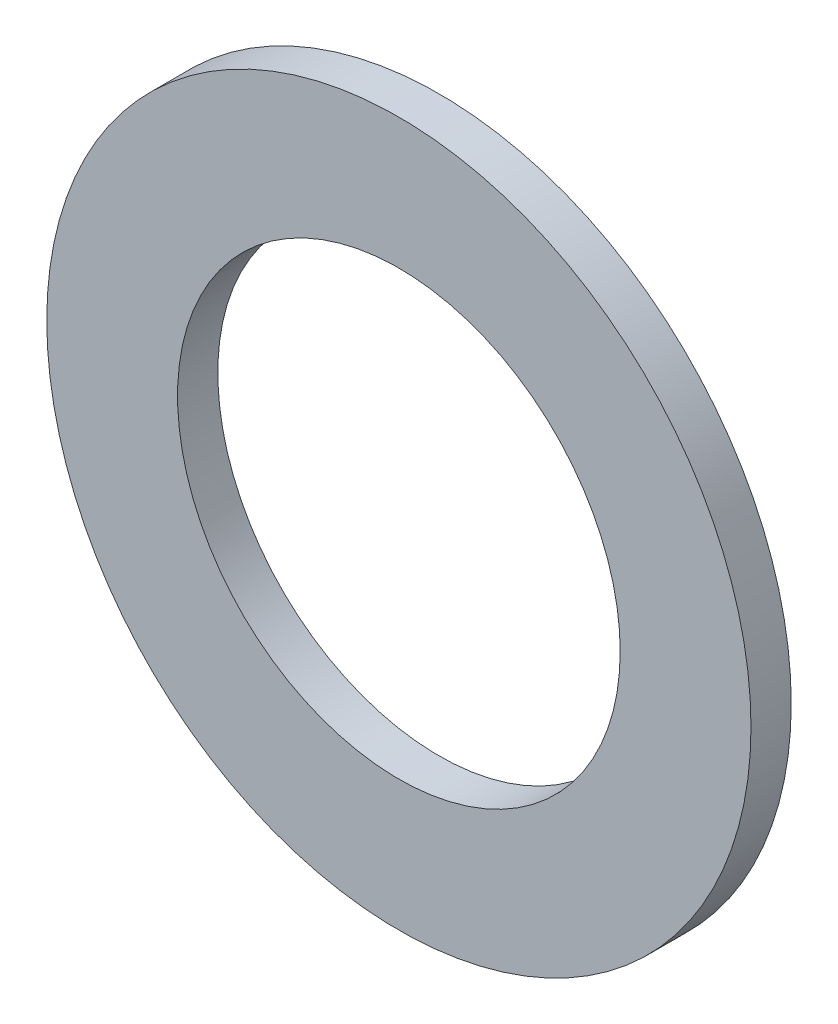
SolidWorks part; units mm, degrees
material "Резина"
ref_plane "Спереди" through (0, 0, 0) normal (0, 0, 1) x (1, 0, 0)
ref_plane "Сверху" through (0, 0, 0) normal (0, 1, 0) x (1, 0, 0)
ref_plane "Справа" through (0, 0, 0) normal (1, 0, 0) x (0, 0, -1)
sketch "Эскиз1" plane through (0, 0, 0) normal (0, 0, 1) x (1, 0, 0)
  circle A1 centre (-25, 0) radius 17.5
  circle A2 centre (-25, 0) radius 17.5
  circle A3 centre (-25, 0) radius 11
  dimension "D2" = 22
  dimension "D1" = 0
extrude "Бобышка-Вытянуть1" add sketch "Эскиз1" along normal blind 2
